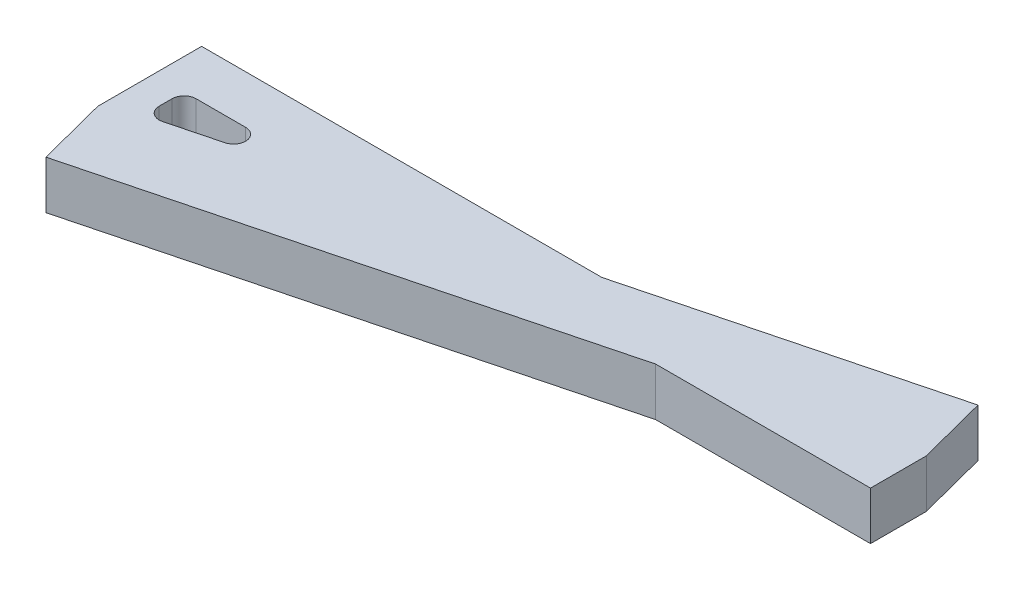
SolidWorks part; units mm, degrees
ref_plane "Front Plane" through (0, 0, 0) normal (0, 0, 1) x (1, 0, 0)
ref_plane "Top Plane" through (0, 0, 0) normal (0, 1, 0) x (1, 0, 0)
ref_plane "Right Plane" through (0, 0, 0) normal (1, 0, 0) x (0, 0, -1)
sketch "Sketch1" plane through (0, 0, 0) normal (0, 1, 0) x (1, 0, 0)
  line L0 (-1000, 0) -> (49000, 0) construction
  line L1 (0, 0) -> (20.1128, 5.2203)
  line L2 (29.0379, 7.5367) -> (28.2842, 10.4405)
  line L3 (28.2842, 10.4405) -> (15.877, 7.2203)
  line L4 (-0.7537, 2.9038) -> (0, 0)
  line L5 (-0.3768, 1.4519) -> (28.661, 8.9886) construction
  line L6 (20.1128, 5.2203) -> (29.0379, 5.2203)
  line L7 (0.5169, 4.7203) -> (0.5169, 4.1863)
  line L8 (-0.7537, 5.2203) -> (-0.7537, 7.2203)
  line L9 (-0.7537, 7.2203) -> (15.877, 7.2203)
  line L10 (29.0379, 7.2203) -> (29.0379, 5.2203)
  line L11 (29.0379, 7.2203) -> (29.0379, 7.5367)
  line L12 (-0.7537, 5.2203) -> (-0.7537, 2.9038)
  line L13 (1.1425, 3.7023) -> (3.2, 4.2363)
  line L14 (3.0744, 5.2203) -> (1.0169, 5.2203)
  arc A0 (3.2, 4.2363) -> (3.0744, 5.2203) centre (3.0744, 4.7203) ccw
  arc A1 (1.1425, 3.7023) -> (0.5169, 4.1863) centre (1.0169, 4.1863) cw
  arc A2 (1.0169, 5.2203) -> (0.5169, 4.7203) centre (1.0169, 4.7203) ccw
  dimension "D2" = 0.5
  dimension "D3" = 0.5
  dimension "D4" = 0.5
  dimension "D1" = 14.55
extrude "Boss-Extrude1" add sketch "Sketch1" along normal blind 2
